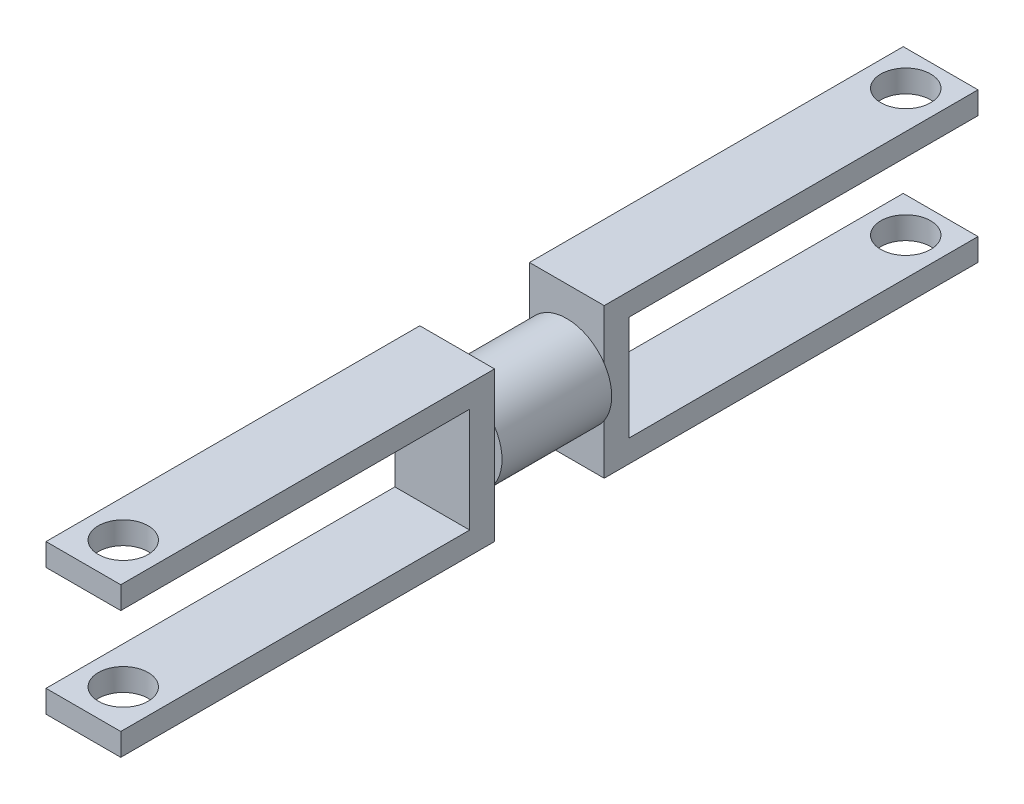
SolidWorks part; units mm, degrees
ref_plane "前视基准面" through (0, 0, 0) normal (0, 0, 1) x (1, 0, 0)
ref_plane "上视基准面" through (0, 0, 0) normal (0, 1, 0) x (1, 0, 0)
ref_plane "右视基准面" through (0, 0, 0) normal (1, 0, 0) x (0, 0, -1)
sketch "草图1" plane through (0, 0, 0) normal (0, 0, 1) x (1, 0, 0)
  circle A0 centre (0, 0) radius 3.6
extrude "凸台-拉伸1" add sketch "草图1" along normal blind 8.8
sketch "草图2" plane through (0, 0, 8.8) normal (0, 0, 1) x (1, 0, 0)
  line L1 (-3, -6) -> (3, -6)
  line L2 (-3, -6) -> (-3, 6)
  line L3 (-3, 6) -> (3, 6)
  line L4 (3, -6) -> (3, 6)
  line L5 (-3, -6) -> (3, 6) construction
  line L6 (-3, 6) -> (3, -6) construction
  point P0 (0, 0)
extrude "凸台-拉伸2" add sketch "草图2" along normal blind 30
sketch "草图4" plane through (0, 0, 0) normal (0, 0, -1) x (-1, 0, 0)
  line L1 (-3, 6) -> (3, 6)
  line L2 (-3, 6) -> (-3, -6)
  line L3 (-3, -6) -> (3, -6)
  line L4 (3, 6) -> (3, -6)
  line L5 (-3, 6) -> (3, -6) construction
  line L6 (-3, -6) -> (3, 6) construction
  point P0 (0, 0)
extrude "凸台-拉伸3" add sketch "草图4" along normal blind 30
sketch "草图3" plane through (0, 6, 0) normal (0, 1, 0) x (1, 0, 0)
  line L0 (0, -38.8) -> (0, -35.6)
  line L1 (3, -38.8) -> (-3, -38.8) construction
  line L2 (0, 30) -> (0, 27.2)
  line L3 (-3, 30) -> (3, 30) construction
  circle A0 centre (0, -35.6) radius 2
  circle A1 centre (0, 27.2) radius 2
extrude "切除-拉伸1" cut sketch "草图3" against normal blind 30
sketch "草图5" plane through (0, 0, -30) normal (0, 0, -1) x (-1, 0, 0)
  line L0 (-3, -4.2) -> (3, -4.2)
  line L1 (-3, -4.2) -> (-3, 4.2)
  line L2 (3, -4.2) -> (3, 4.2)
  line L3 (-3, 4.2) -> (3, 4.2)
  line L4 (-3, -4.2) -> (3, 4.2) construction
  line L5 (3, -4.2) -> (-3, 4.2) construction
  point P1 (0, 0)
extrude "切除-拉伸2" cut sketch "草图5" against normal blind 28
sketch "草图6" plane through (0, 0, 38.8) normal (0, 0, 1) x (1, 0, 0)
  line L0 (-3, -4.2) -> (3, -4.2)
  line L1 (-3, -4.2) -> (-3, 4.2)
  line L2 (3, -4.2) -> (3, 4.2)
  line L3 (-3, 4.2) -> (3, 4.2)
  line L4 (-3, -4.2) -> (3, 4.2) construction
  line L5 (3, -4.2) -> (-3, 4.2) construction
  point P1 (0, 0)
extrude "切除-拉伸3" cut sketch "草图6" against normal blind 28
